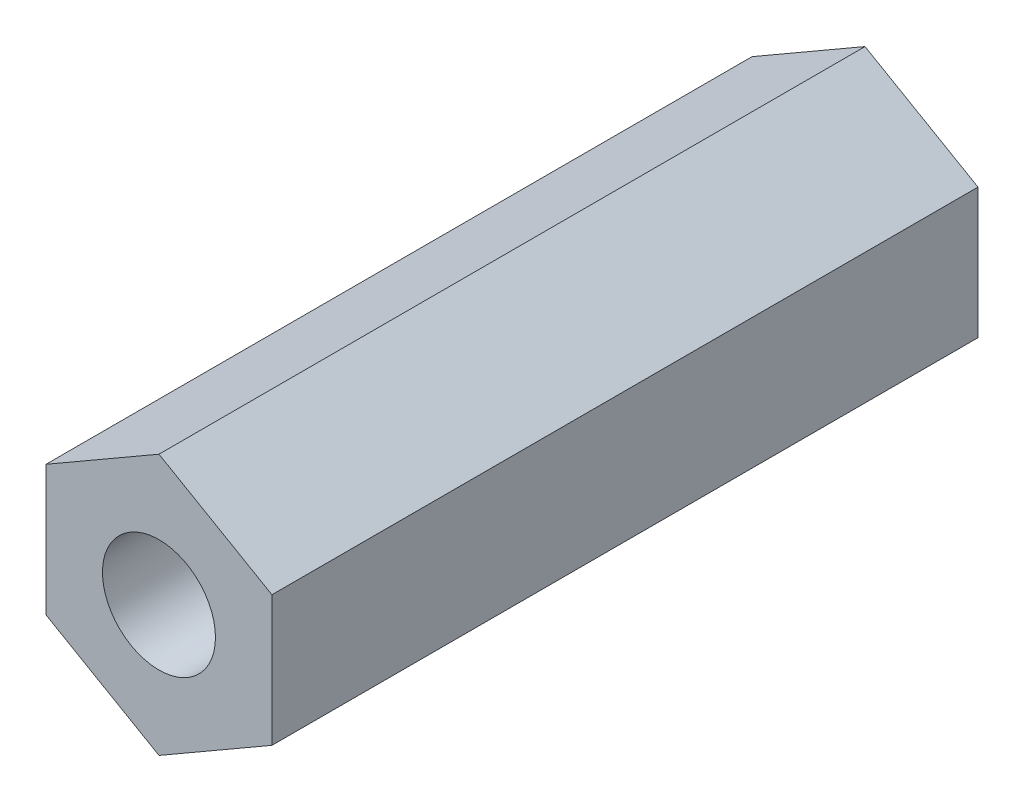
SolidWorks part; units mm, degrees
ref_plane "Front" through (0, 0, 0) normal (0, 0, 1) x (1, 0, 0)
ref_plane "Top" through (0, 0, 0) normal (0, 1, 0) x (1, 0, 0)
ref_plane "Right" through (0, 0, 0) normal (1, 0, 0) x (0, 0, -1)
sketch "Esquisse1" plane through (0, 0, 0) normal (0, 0, 1) x (1, 0, 0)
  line L1 (4, -2.3094) -> (4, 2.3094)
  line L2 (4, 2.3094) -> (0, 4.6188)
  line L3 (0, 4.6188) -> (-4, 2.3094)
  line L4 (-4, 2.3094) -> (-4, -2.3094)
  line L5 (-4, -2.3094) -> (0, -4.6188)
  line L6 (0, -4.6188) -> (4, -2.3094)
  circle A0 centre (0, 0) radius 2
  circle A1 centre (0, 0) radius 4 construction
  dimension "D1" = 4
  dimension "D2" = 8
extrude "Boss.-Extru.1" add sketch "Esquisse1" along normal blind 25
